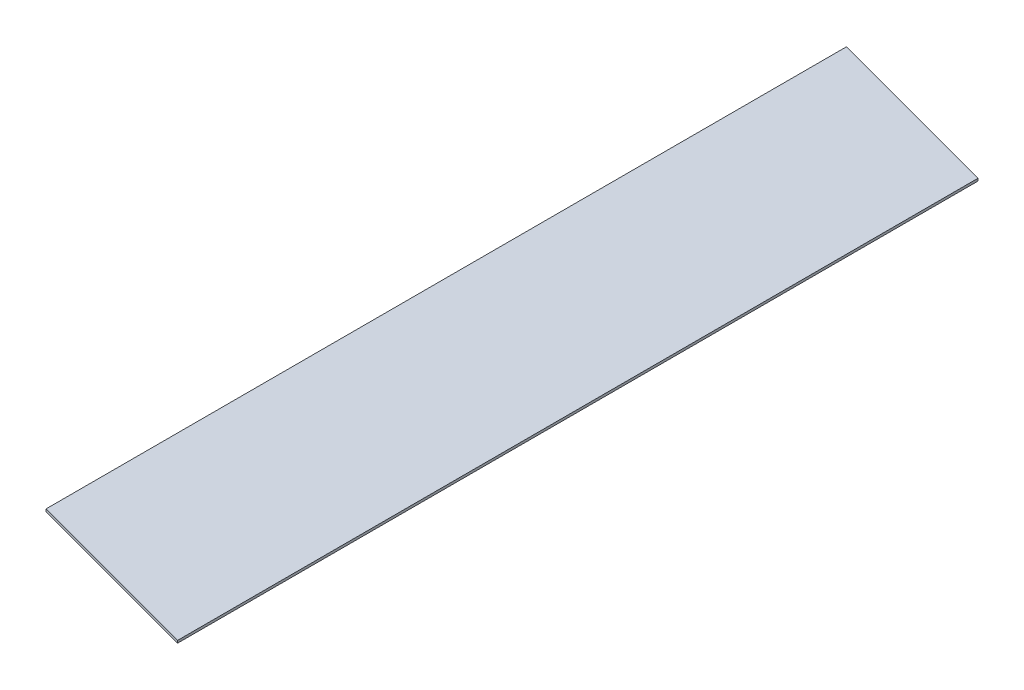
SolidWorks part; units mm, degrees
ref_plane "Front Plane" through (0, 0, 0) normal (0, 0, 1) x (1, 0, 0)
ref_plane "Top Plane" through (0, 0, 0) normal (0, 1, 0) x (1, 0, 0)
ref_plane "Right Plane" through (0, 0, 0) normal (1, 0, 0) x (0, 0, -1)
sketch "Sketch1" plane through (0, 0, 0) normal (0, 1, 0) x (1, 0, 0)
  line L1 (-90.4488, 82.5345) -> (94.9712, 82.5345)
  line L2 (-90.4488, 82.5345) -> (-90.4488, -743.7275)
  line L3 (-90.4488, -743.7275) -> (94.9712, -743.7275)
  line L4 (94.9712, 82.5345) -> (94.9712, -743.7275)
  dimension "D1" = 185.42
  dimension "D2" = 826.262
extrude "Boss-Extrude1" add sketch "Sketch1" along normal blind 2.54
sketch "Sketch2" plane through (0, 2.54, 0) normal (0, 1, 0) x (1, 0, 0)
  line L0 (94.9712, -743.7275) -> (-90.4488, -694.0443)
  line L2 (-90.4488, 82.5345) -> (-90.4488, -743.7275) construction
  line L3 (-90.4488, -694.0443) -> (-90.4488, -743.7275)
  line L4 (-90.4488, -743.7275) -> (94.9712, -743.7275)
  dimension "D1" = 15
extrude "Cut-Extrude1" cut sketch "Sketch2" against normal blind 2.54
sketch "Sketch3" plane through (0, 0, 0) normal (0, -1, 0) x (1, 0, 0)
  line L0 (-90.4488, -82.5345) -> (-90.4488, -132.2177)
  line L1 (-90.4488, -132.2177) -> (94.9712, -82.5345)
  line L2 (94.9712, -82.5345) -> (-90.4488, -82.5345) construction
  line L7 (94.9712, -82.5345) -> (94.9712, 743.7275)
  line L8 (94.9712, 743.7275) -> (-90.4488, 694.0443)
  line L9 (-90.4488, 694.0443) -> (-90.4488, -82.5345)
  line L10 (-90.4488, -82.5345) -> (94.9712, -82.5345)
  line L14 (-90.4488, -82.5345) -> (94.9712, -82.5345)
  dimension "D1" = 15
  dimension "D2" = 0
extrude "Boss-Extrude3" add sketch "Sketch3" against normal blind 2.54
